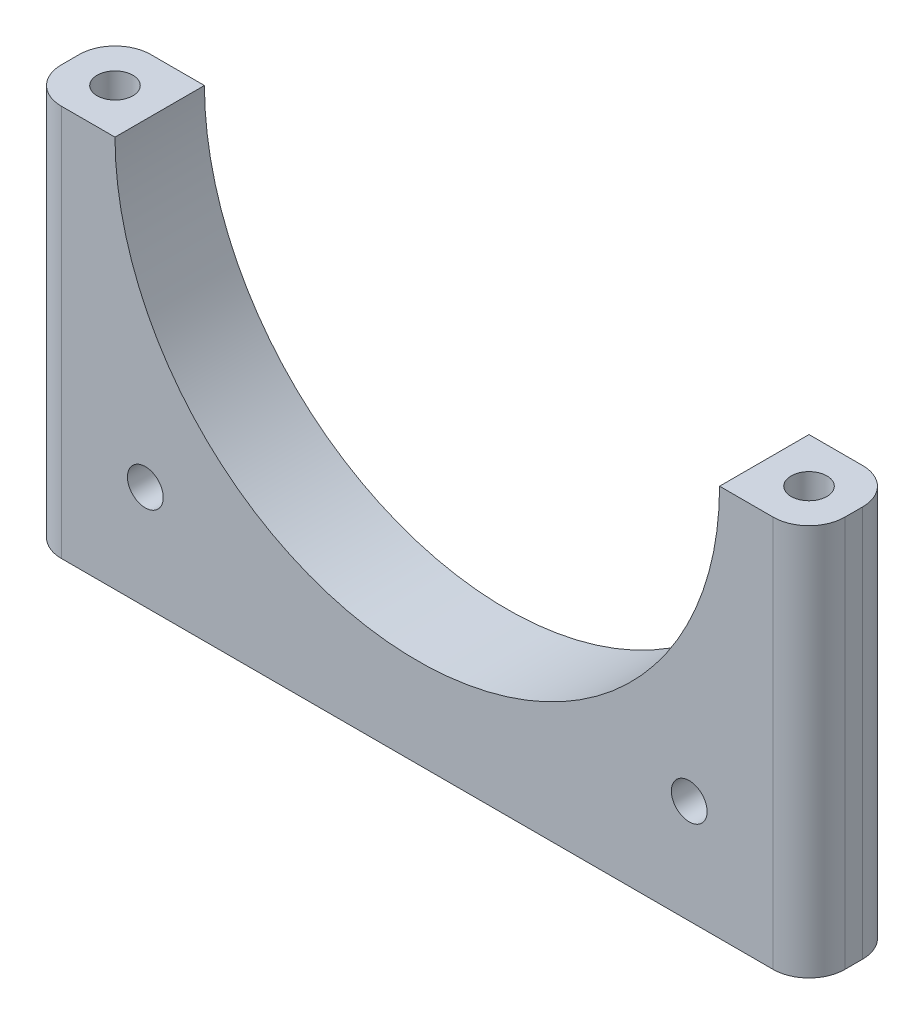
SolidWorks part; units mm, degrees
ref_plane "Front Plane" through (0, 0, 0) normal (0, 0, 1) x (1, 0, 0)
ref_plane "Top Plane" through (0, 0, 0) normal (0, 1, 0) x (1, 0, 0)
ref_plane "Right Plane" through (0, 0, 0) normal (1, 0, 0) x (0, 0, -1)
sketch "Sketch4" plane through (0, 0, 0) normal (0, 0, 1) x (1, 0, 0)
  line L0 (0, 0) -> (0, 169)
  line L1 (-84.5, 84.5) -> (84.5, 84.5)
  line L2 (0, 0) -> (0, 194)
  line L3 (-109.5, 84.5) -> (-109.5, -25)
  line L4 (109.5, 84.5) -> (109.5, -25)
  line L5 (109.5, -25) -> (0, -25)
  line L6 (0, -25) -> (-109.5, -25)
  line L7 (-109.5, 84.5) -> (109.5, 84.5)
  circle A0 centre (0, 84.5) radius 84.5
  circle A1 centre (0, 84.5) radius 109.5
  dimension "D1" = 169
  dimension "D2" = 25
extrude "Boss-Extrude1" add sketch "Sketch4" along normal blind 25 contours A1 L3 L6 | L7 A1 A0 | A1 L5 L4
sketch "Sketch5" plane through (0, 84.5, 0) normal (0, 1, 0) x (1, 0, 0)
  line L0 (0, 0) -> (0, -33.3515) construction
  line L1 (-109.5, 0) -> (-84.5, 0) construction
  line L2 (-109.5, -25) -> (-109.5, 0) construction
  circle A0 centre (-97, -12.5) radius 5
  circle A1 centre (97, -12.5) radius 5
  dimension "D1" = 10
  dimension "D2" = 12.5
  dimension "D3" = 12.5
extrude "Cut-Extrude1" cut sketch "Sketch5" against normal blind 5000 contours A0 | A1
sketch "Sketch6" plane through (0, 0, 25) normal (0, 0, 1) x (1, 0, 0)
  line L0 (-84.5, 84.5) -> (-84.5, -25)
  line L1 (109.5, -25) -> (-109.5, -25) construction
  line L3 (0, 0) -> (0, -39.0782) construction
  line L4 (0, 3.99) -> (-76.015, 3.99) construction
  line L5 (-76.015, 3.99) -> (0, 3.99) construction
  line L6 (0, 3.99) -> (76.015, 3.99) construction
  arc A0 (-84.5, 84.5) -> (84.5, 84.5) centre (0, 84.5) ccw construction
  circle A1 centre (-76.015, 3.99) radius 5
  circle A2 centre (76.015, 3.99) radius 5
  dimension "D1" = 10
  dimension "D2" = 152.03
  dimension "D3" = 28.99
extrude "Cut-Extrude2" cut sketch "Sketch6" against normal blind 5000
fillet "Fillet2" radius 10 4 edges at (109.5, 29.75, 25) (109.5, 29.75, 0) (-109.5, 29.75, 25) (-109.5, 29.75, 0)
